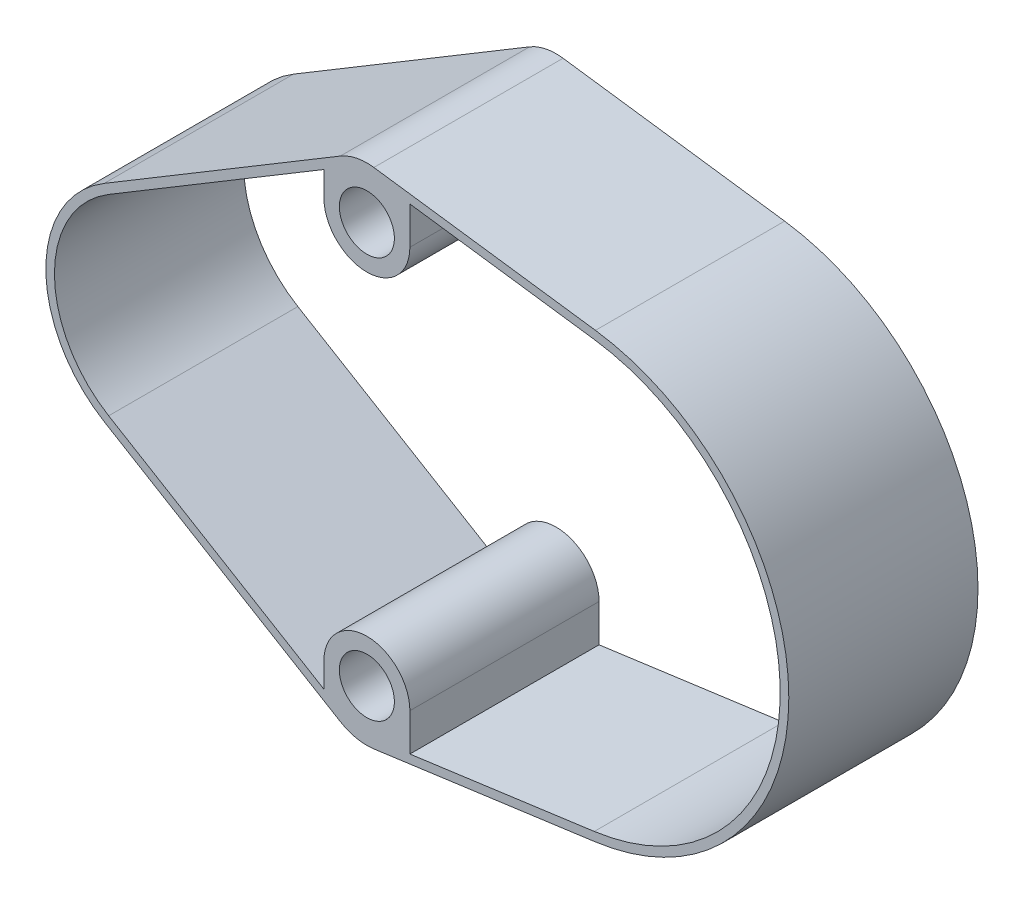
SolidWorks part; units mm, degrees
ref_plane "Front" through (0, 0, 0) normal (0, 0, 1) x (1, 0, 0)
ref_plane "Top" through (0, 0, 0) normal (0, 1, 0) x (1, 0, 0)
ref_plane "Right" through (0, 0, 0) normal (1, 0, 0) x (0, 0, -1)
sketch "Sketch1" plane through (0, 0, 0) normal (0, 0, 1) x (1, 0, 0)
  line L9 (12.0731, 14.6397) -> (24.9585, 12.8805)
  line L15 (12.0731, -14.6397) -> (24.9585, -12.8805)
  line L16 (11.6673, 14.6673) -> (-11.6673, 14.6673)
  line L17 (11.6673, -14.6673) -> (0, -14.6673)
  line L18 (-14.3958, 12.9144) -> (-19.7285, 1.2471)
  line L19 (-18.6976, -2.4735) -> (-1.6976, -14.1408)
  circle A17 centre (0, 0) radius 3
  circle A18 centre (23.2, 0) radius 4.5
  circle A19 centre (8.6, 0) radius 3
  circle A24 centre (-17, 0) radius 1.6
  arc A26 (12.0731, 14.6397) -> (11.6673, 14.6673) centre (11.6673, 11.6673) ccw
  arc A28 (-11.6673, 14.6673) -> (-14.3958, 12.9144) centre (-11.6673, 11.6673) ccw
  arc A29 (11.6673, -14.6673) -> (12.0731, -14.6397) centre (11.6673, -11.6673) ccw
  arc A30 (-1.6976, -14.1408) -> (0, -14.6673) centre (0, -11.6673) ccw
  arc A31 (-19.7285, 1.2471) -> (-18.6976, -2.4735) centre (-17, 0) ccw
  circle A32 centre (0, -11.6673) radius 1.6
  circle A33 centre (11.6673, -11.6673) radius 1.6
  circle A34 centre (-11.6673, 11.6673) radius 1.6
  circle A35 centre (0, 11.6673) radius 1.6
  circle A36 centre (11.6673, 11.6673) radius 1.6
  arc A37 (24.9585, -12.8805) -> (24.9585, 12.8805) centre (23.2, 0) ccw
extrude "Boss-Extrude3" add sketch "Sketch1" along normal blind 1.6
sketch "Sketch2" plane through (0, 0, 1.6) normal (0, 0, 1) x (1, 0, 0)
  line L0 (12.0731, 14.6397) -> (24.9585, 12.8805)
  line L1 (12.0731, -14.6397) -> (24.9585, -12.8805)
  line L2 (9.8187, 14.0301) -> (-3.0809, 3.938)
  line L4 (9.8187, -14.0301) -> (-3.0809, -3.938)
  arc A0 (24.9585, -12.8805) -> (24.9585, 12.8805) centre (23.2, 0) ccw
  arc A1 (-3.0809, 3.938) -> (-3.0809, -3.938) centre (0, 0) ccw
  arc A2 (12.0731, 14.6397) -> (9.8187, 14.0301) centre (11.6673, 11.6673) ccw
  arc A3 (9.8187, -14.0301) -> (12.0731, -14.6397) centre (11.6673, -11.6673) ccw
  circle A4 centre (11.6673, 11.6673) radius 1.6
  circle A5 centre (0, 0) radius 3
  circle A6 centre (8.6, 0) radius 3
  circle A7 centre (23.2, 0) radius 4.5
  circle A8 centre (11.6673, -11.6673) radius 1.6
extrude "Boss-Extrude4" add sketch "Sketch2" along normal blind 1.5
sketch "Sketch3" plane through (0, 0, 0) normal (0, 0, -1) x (-1, 0, 0)
  circle A0 centre (0, 0) radius 63.2066
extrude "Cut-Extrude1" cut sketch "Sketch3" against normal blind 1.6
sketch "Sketch4" plane through (0, 0, 3.1) normal (0, 0, 1) x (1, 0, 0)
  line L0 (-3.6022, 6.002) -> (10.1235, 14.2396)
  line L1 (14.6673, 11.6673) -> (14.6673, -11.6673)
  line L2 (-3.6022, -6.002) -> (10.1235, -14.2396)
  arc A0 (14.6673, 11.6673) -> (10.1235, 14.2396) centre (11.6673, 11.6673) ccw
  arc A1 (10.1235, -14.2396) -> (14.6673, -11.6673) centre (11.6673, -11.6673) ccw
  arc A2 (-3.6022, 6.002) -> (-3.6022, -6.002) centre (0, 0) ccw
  circle A3 centre (0, 0) radius 3
  circle A4 centre (8.6, 0) radius 3
  circle A5 centre (11.6673, 11.6673) radius 1.6
  circle A6 centre (11.6673, -11.6673) radius 1.6
extrude "Boss-Extrude5" add sketch "Sketch4" against normal up to surface (1.5 mm away) up to face at (-3, 0, 1.6)
sketch "Sketch5" plane through (0, 0, 3.1) normal (0, 0, 1) x (1, 0, 0)
  line L0 (-3.6022, 6.002) -> (10.1235, 14.2396)
  line L1 (12.0731, 14.6397) -> (24.9585, 12.8805)
  line L2 (-3.6022, -6.002) -> (10.1235, -14.2396)
  line L3 (12.0731, -14.6397) -> (24.9585, -12.8805)
  line L5 (3.5176, 9.6927) -> (-3.3453, 5.5734)
  line L7 (23.2, 0) -> (16.182, 0)
  line L9 (18.3336, 13.2803) -> (24.8909, 12.3851)
  line L10 (24.8909, 12.3851) -> (14.1673, 13.8491)
  line L11 (24.8909, -12.3851) -> (14.1673, -13.8491)
  line L12 (18.3336, -13.2803) -> (24.8909, -12.3851)
  line L14 (-3.3453, -5.5734) -> (9.1673, -13.0839)
  line L15 (3.5176, -9.6927) -> (-3.3453, -5.5734)
  line L17 (12.0731, -14.6397) -> (24.9585, -12.8805)
  line L18 (-3.6022, -6.002) -> (10.1235, -14.2396)
  line L19 (14.1673, 11.6673) -> (14.1673, 13.8491)
  line L20 (9.1673, 11.6673) -> (9.1673, 13.0839)
  line L21 (9.1673, -11.6673) -> (9.1673, -13.0839)
  line L22 (14.1673, -11.6673) -> (14.1673, -13.8491)
  line L24 (-3.3453, 5.5734) -> (9.1673, 13.0839)
  arc A0 (-3.6022, 6.002) -> (-3.6022, -6.002) centre (0, 0) ccw
  arc A1 (24.9585, -12.8805) -> (24.9585, 12.8805) centre (23.2, 0) ccw
  arc A2 (12.0731, 14.6397) -> (10.1235, 14.2396) centre (11.6673, 11.6673) ccw
  arc A3 (10.1235, -14.2396) -> (12.0731, -14.6397) centre (11.6673, -11.6673) ccw
  arc A4 (-3.3453, 5.5734) -> (-3.3453, -5.5734) centre (0, 0) ccw
  arc A5 (24.8909, -12.3851) -> (24.8909, 12.3851) centre (23.2, 0) ccw
  circle A7 centre (11.6673, 11.6673) radius 1.6
  arc A8 (9.1673, 11.6673) -> (14.1673, 11.6673) centre (11.6673, 11.6673) ccw
  arc A9 (9.1673, -11.6673) -> (14.1673, -11.6673) centre (11.6673, -11.6673) cw
  circle A10 centre (11.6673, -11.6673) radius 1.6
  arc A11 (12.0731, -14.6397) -> (10.1235, -14.2396) centre (11.6673, -11.6673) cw
  line M10 (-3.6022, -6.002) -> (10.1235, -14.2396)
  arc M11 (10.1235, -14.2396) -> (12.0731, -14.6397) centre (11.6673, -11.6673) ccw
  line M12 (12.0731, -14.6397) -> (24.9585, -12.8805)
  arc M13 (24.9585, -12.8805) -> (24.9585, 12.8805) centre (23.2, 0) ccw
  line M14 (24.9585, 12.8805) -> (12.0731, 14.6397)
  arc M15 (12.0731, 14.6397) -> (10.1235, 14.2396) centre (11.6673, 11.6673) ccw
  line M16 (10.1235, 14.2396) -> (-3.6022, 6.002)
  arc M17 (-3.6022, 6.002) -> (-3.6022, -6.002) centre (0, 0) ccw
  circle M19 centre (11.6673, -11.6673) radius 1.6
  circle M21 centre (11.6673, 11.6673) radius 1.6
extrude "Boss-Extrude6" add sketch "Sketch5" along normal blind 11 contours A9 L21 L14 A4 L5 L24 L20 A8 L19 L10 L9 A5 L11 L22 M17 M10 M11 M12 M13 M14 M15 M16 M21 M19
sketch "Sketch6" plane through (0, 0, 1.6) normal (0, 0, -1) x (-1, 0, 0)
  circle A0 centre (0, 0) radius 49.5144
extrude "Cut-Extrude2" cut sketch "Sketch6" against normal up to surface (1.5 mm away) up to face at (12.0069, 0, 3.1)
